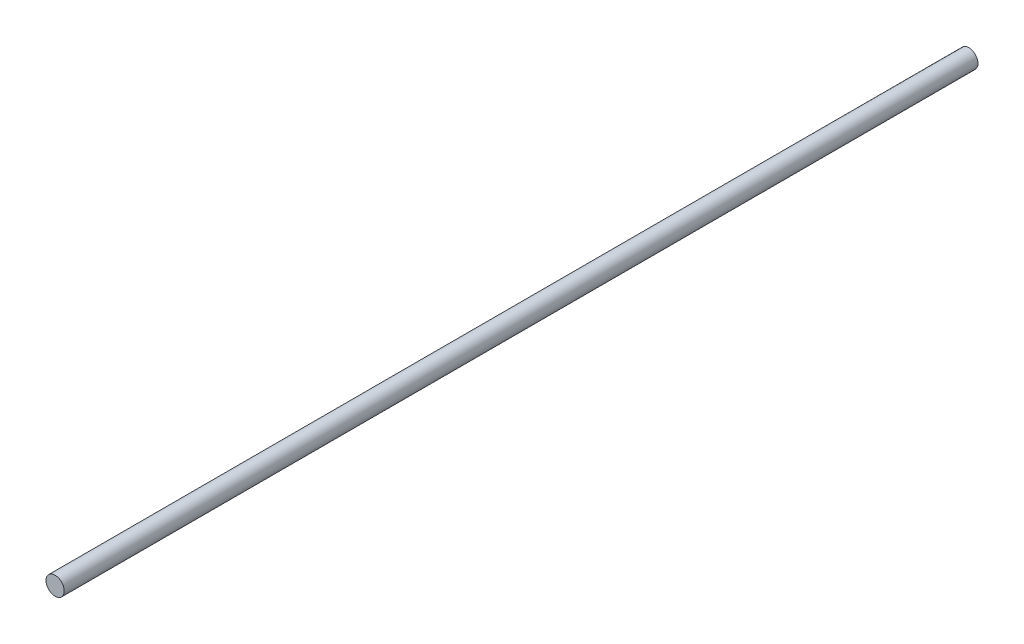
SolidWorks part; units mm, degrees
ref_plane "前视基准面" through (0, 0, 0) normal (0, 0, 1) x (1, 0, 0)
ref_plane "上视基准面" through (0, 0, 0) normal (0, 1, 0) x (1, 0, 0)
ref_plane "右视基准面" through (0, 0, 0) normal (1, 0, 0) x (0, 0, -1)
sketch "草图1" plane through (0, 0, 0) normal (0, 0, 1) x (1, 0, 0)
  circle A0 centre (0, 0) radius 2
  dimension "D1" = 4
extrude "凸台-拉伸1" add sketch "草图1" along normal blind 200
